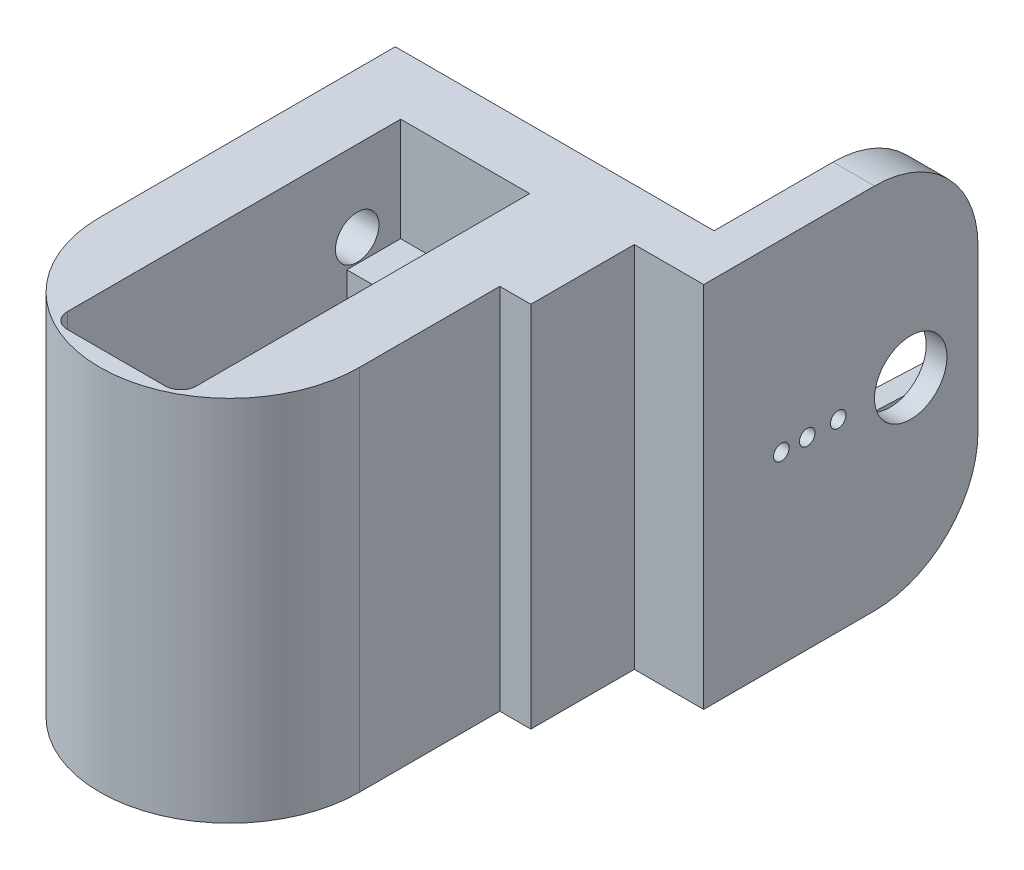
SolidWorks part; units mm, degrees
ref_plane "Front Plane" through (0, 0, 0) normal (0, 0, 1) x (1, 0, 0)
ref_plane "Top Plane" through (0, 0, 0) normal (0, 1, 0) x (1, 0, 0)
ref_plane "Right Plane" through (0, 0, 0) normal (1, 0, 0) x (0, 0, -1)
sketch "Sketch4" plane through (0, 0, 0) normal (0, 0, 1) x (1, 0, 0)
  line L1 (-6.23, -9.975) -> (6.23, -9.975)
  line L2 (-6.23, -9.975) -> (-6.23, 7.275)
  line L3 (-6.23, 7.275) -> (6.23, 7.275)
  line L4 (6.23, -9.975) -> (6.23, 7.275)
  point P4 (0, 7.275)
  dimension "D1" = 12.46
  dimension "D2" = 17.25
  dimension "D3" = 9.975
extrude "Boss-Extrude3" add sketch "Sketch4" along normal blind 6
sketch "Sketch8" plane through (0, -9.975, 0) normal (0, -1, 0) x (-1, 0, 0)
  circle A0 centre (0, -23.55) radius 12.5468
  circle A1 centre (0, -23.55) radius 11.15
  dimension "D1" = 22.3
  dimension "D2" = 23.55
extrude "Boss-Extrude6" add sketch "Sketch8" along normal blind 8.3 and the other way up to surface (17.25 mm away) other way up to face at (0, 7.275, 3)
sketch "Sketch5" plane through (0, 7.275, 0) normal (0, 1, 0) x (1, 0, 0)
  line L8 (12.5468, -23.55) -> (12.5468, 0)
  line L9 (12.5468, 0) -> (6.23, 0)
  line L10 (-12.5468, -23.55) -> (-12.5468, 0)
  line L11 (-12.5468, 0) -> (-6.23, 0)
  line L12 (-6.23, 0) -> (-6.23, -29.7)
  line L14 (6.23, -29.7) -> (6.23, 0)
  line L15 (-6.23, -29.7) -> (6.23, -29.7)
  line L16 (6.23, -6) -> (-6.23, -6) construction
  circle A0 centre (0, -23.55) radius 12.5468 construction
  arc A1 (-12.5468, -23.55) -> (12.5468, -23.55) centre (0, -23.55) ccw
  dimension "D1" = 23.7
  dimension "D2" = 23.55
extrude "Boss-Extrude4" add sketch "Sketch5" against normal up to surface (17.25 mm away) up to face at (0, -9.975, 3)
sketch "Sketch6" plane through (0, 7.275, 0) normal (0, 1, 0) x (1, 0, 0)
  line L0 (6.23, -6) -> (-6.23, -6) construction
  line L3 (6.23, -29.7) -> (-6.23, -29.7) construction
  circle A0 centre (0, -3.6) radius 0.75
  circle A1 centre (0, -32.1) radius 0.75
  dimension "D1" = 1.5
  dimension "D3" = 1.5
  dimension "D2" = 2.4
  dimension "D4" = 2.4
extrude "Cut-Extrude1" cut sketch "Sketch6" against normal blind 5
chamfer "Chamfer1" distance 0.5 angle 60 2 edges at (0, 7.275, 4.35) (0, 7.275, 32.85)
sketch "Sketch10" plane through (0, 7.275, 0) normal (0, 1, 0) x (1, 0, 0)
  line L1 (-6.23, -6) -> (6.23, -6)
  line L2 (-6.23, -6) -> (-6.23, -29.7)
  line L3 (-6.23, -29.7) -> (6.23, -29.7)
  line L4 (6.23, -6) -> (6.23, -29.7)
extrude "Cut-Extrude3" cut sketch "Sketch10" against normal up to surface (17.25 mm away) up to face at (0, -9.975, 27.1007)
ref_plane "Plane1" through (0, 0, 36.0968) normal (0, 0, 1) x (1, 0, 0)
sketch "Sketch13" plane through (0, -18.275, 0) normal (0, -1, 0) x (1, 0, 0)
  line L0 (-12.5468, 23.55) -> (-12.5468, 0)
  line L1 (-12.5468, 0) -> (12.5468, 0)
  line L2 (12.5468, 0) -> (12.5468, 23.55)
  arc A0 (-12.5468, 23.55) -> (12.5468, 23.55) centre (0, 23.55) ccw
  point P3 (0, 0)
extrude "Boss-Extrude7" add sketch "Sketch13" against normal up to surface (8.3 mm away) up to face at (0, -9.975, 27.1007)
sketch "Sketch15" plane through (0, 7.275, 0) normal (0, 1, 0) x (1, 0, 0)
  line L0 (-12.5468, 0) -> (12.5468, 0)
  line L1 (12.5468, 0) -> (12.5468, -23.55)
  line L2 (-12.5468, 0) -> (-12.5468, -23.55)
  line L3 (6.23, -6) -> (6.23, -29.7) construction
  line L4 (-6.23, -0.8) -> (6.23, -0.8)
  line L5 (-6.23, -0.8) -> (-6.23, -33)
  line L6 (-4.73, -34.5) -> (4.73, -34.5)
  line L7 (6.23, -0.8) -> (6.23, -33)
  arc A0 (-12.5468, -23.55) -> (12.5468, -23.55) centre (0, -23.55) ccw
  circle A1 centre (0, -3.6) radius 0.75 construction
  arc A2 (4.73, -34.5) -> (6.23, -33) centre (4.73, -33) ccw
  arc A3 (-6.23, -33) -> (-4.73, -34.5) centre (-4.73, -33) ccw
  point P15 (0, -0.8)
  dimension "D1" = 0.8
  dimension "D3" = 1.5
  dimension "D2" = 2.8
  dimension "D4" = 0
  dimension "D5" = 34.5
extrude "Boss-Extrude9" add sketch "Sketch15" along normal blind 10
sketch "Sketch20" plane through (0, -18.275, 0) normal (0, -1, 0) x (1, 0, 0)
  circle A0 centre (0, 23.55) radius 7.15
  circle A1 centre (0, 23.55) radius 11.15
  circle A2 centre (0, 23.55) radius 11.15 construction
  dimension "D1" = 14.3
extrude "Boss-Extrude11" add sketch "Sketch20" against normal up to surface (8.3 mm away) up to face at (0, -9.975, 27.1007)
sketch "Sketch21" plane through (0, -18.275, 0) normal (0, -1, 0) x (1, 0, 0)
  circle A0 centre (0, 23.55) radius 7.15
  circle A1 centre (0, 23.55) radius 10.15
  circle A2 centre (0, 23.55) radius 7.15 construction
  dimension "D1" = 20.3
extrude "Cut-Extrude7" cut sketch "Sketch21" against normal blind 1.3
sketch "Sketch11" plane through (0, 0, 29.7) normal (0, 0, 1) x (1, 0, 0)
  line L1 (-5, -9.975) -> (5, -9.975)
  line L2 (-5, -9.975) -> (-5, -11.975)
  line L3 (-5, -11.975) -> (5, -11.975)
  line L4 (5, -9.975) -> (5, -11.975)
  line L5 (-3.6469, -9.975) -> (3.6469, -9.975) construction
  point P4 (0, -9.975)
  dimension "D1" = 0
  dimension "D2" = 10
  dimension "D3" = 2
extrude "Cut-Extrude4" cut sketch "Sketch11" against normal up to surface (23.7 mm away) up to face at (0, -1.35, 6)
sketch "Sketch25" plane through (0, -18.275, 0) normal (0, -1, 0) x (1, 0, 0)
  line L0 (6.23, 20.0415) -> (6.23, 6) construction
  line L1 (-6.23, 6) -> (6.23, 6)
  line L2 (-6.23, 6) -> (-6.23, 12)
  line L3 (-6.23, 12) -> (6.23, 12)
  line L4 (6.23, 6) -> (6.23, 12)
  dimension "D1" = 6
extrude "Cut-Extrude8" cut sketch "Sketch25" against normal up to next
sketch "Sketch17" plane through (0, 17.275, 0) normal (0, 1, 0) x (1, 0, 0)
  line L0 (22.25, 26.5) -> (22.25, 0)
  line L1 (22.25, 0) -> (-22.25, 0)
  line L2 (-22.25, 0) -> (-22.25, 26.5)
  line L3 (-22.25, 26.5) -> (-18.25, 26.5)
  line L4 (-18.25, 26.5) -> (-18.25, 5)
  line L5 (-18.25, 5) -> (18.25, 5)
  line L6 (18.25, 5) -> (18.25, 26.5)
  line L7 (18.25, 26.5) -> (22.25, 26.5)
  point P2 (0, 5)
  point P10 (0, 0)
  dimension "D1" = 4
  dimension "D2" = 36.5
  dimension "D3" = 0
  dimension "D4" = 26.5
  dimension "D5" = 5
extrude "Boss-Extrude10" add sketch "Sketch17" against normal up to surface (35.55 mm away) up to face at (0, -18.275, 9)
sketch "Sketch18" plane through (18.25, 0, 0) normal (-1, 0, 0) x (0, 0, 1)
  line L0 (-26.5, -18.275) -> (-26.5, 17.275) construction
  line L1 (-26.5, 5.2191) -> (-5, 5.2191)
  line L2 (-26.5, 5.2191) -> (-26.5, -6.2191)
  line L3 (-26.5, -6.2191) -> (-5, -6.2191)
  line L4 (-5, 5.2191) -> (-5, -6.2191)
  line L5 (-5, -18.275) -> (-5, 17.275) construction
  point P6 (-26.5, -0.5)
  point P7 (-26.5, -0.5)
  dimension "D1" = 0
extrude "Cut-Extrude5" cut sketch "Sketch18" against normal blind 2
sketch "Sketch19" plane through (20.25, 0, 0) normal (-1, 0, 0) x (0, 0, 1)
  line L0 (-26.5, -18.275) -> (-26.5, 17.275) construction
  circle A0 centre (-20, -0.5) radius 3.5
  point P4 (-26.5, -0.5)
  dimension "D1" = 7
  dimension "D2" = 6.5
  dimension "D3" = 0
extrude "Cut-Extrude6" cut sketch "Sketch19" against normal through all both and the other way through all
fillet "Fillet1" radius 10 4 edges at (20.25, 17.275, -26.5) (20.25, -18.275, -26.5) (-20.25, 17.275, -26.5) (-20.25, -18.275, -26.5)
ref_plane "Plane2" through (0, 0, 0) normal (1, 0, 0) x (0, 0, -1)
ref_plane "Plane3" through (0, -0.5, 0) normal (0, -1, 0) x (-1, 0, 0)
sketch "Sketch22" plane through (-22.25, 0, 0) normal (-1, 0, 0) x (0, 0, 1)
  circle A0 centre (-20, -0.5) radius 6.5
  dimension "D1" = 13
extrude "Boss-Extrude12" add sketch "Sketch22" against normal blind 5
sketch "Sketch23" plane through (-17.25, 0, 0) normal (1, 0, 0) x (0, 0, -1)
  circle A0 centre (20, -0.5) radius 5.85
  dimension "D1" = 11.7
extrude "Boss-Extrude13" add sketch "Sketch23" along normal blind 5
fillet "Fillet2" radius 1 1 edges at (-12.25, -0.5, -25.85)
sketch "Sketch26" plane through (20.25, 0, 0) normal (-1, 0, 0) x (0, 0, 1)
  line L0 (-5, 2) -> (-20, 2.6585)
  line L1 (-5, -18.275) -> (-5, 17.275) construction
  line L4 (-5, 5.2191) -> (-5, 2)
  line L6 (-26.5, 5.2191) -> (-5, 5.2191)
  line L7 (-20, -3.6585) -> (-5, -3)
  line L8 (-5, -3) -> (-5, -6.2191)
  line L9 (-24.475, -0.5) -> (24.475, -0.5) construction
  line L11 (-26.5, -6.2191) -> (-5, -6.2191)
  line L12 (-20, 2.6585) -> (-26.5, 2.9439)
  line L13 (-20, -3.6585) -> (-26.5, -3.9438)
  line L14 (-26.5, -3.9438) -> (-26.5, -6.2191)
  line L16 (-26.5, 2.9439) -> (-26.5, 5.2191)
  line L18 (-26.5, -8.275) -> (-26.5, 7.275) construction
  circle A0 centre (-20, -0.5) radius 3.5 construction
  dimension "D1" = 5
  dimension "D2" = 2.5
  dimension "D3" = 0
  dimension "D4" = 6.317
  dimension "D5" = 3.1585
  dimension "D6" = 180
  dimension "D7" = 180
extrude "Boss-Extrude14" add sketch "Sketch26" along normal up to surface (2 mm away) up to face at (18.25, 10.8669, -16.3142)
sketch "Sketch27" plane through (22.25, 0, 0) normal (1, 0, 0) x (0, 0, -1)
  line L0 (-24.475, -0.5) -> (24.475, -0.5) construction
  circle A0 centre (10, -0.5) radius 0.75
  circle A1 centre (20, -0.5) radius 3.5 construction
  circle A2 centre (7.5, -0.5) radius 0.75
  circle A3 centre (13, -0.5) radius 0.75
  dimension "D2" = 1.5
  dimension "D4" = 12.5
  dimension "D1" = 10
  dimension "D3" = 7
extrude "Cut-Extrude9" cut sketch "Sketch27" against normal up to next
sketch "Sketch28" plane through (0, -18.275, 0) normal (0, -1, 0) x (1, 0, 0)
  line L0 (-12.5468, 23.55) -> (-12.5468, -11.5534)
  line L5 (-12.5468, -11.5534) -> (-1.7209, -11.5534)
  line L6 (-1.7209, -11.5534) -> (-1.7209, -30.3021)
  line L7 (-1.7209, -30.3021) -> (-26.8097, -30.3021)
  line L8 (-26.8097, -30.3021) -> (-26.8097, 23.55)
  line L9 (-26.8097, 23.55) -> (-12.5468, 23.55)
extrude "Cut-Extrude10" cut sketch "Sketch28" against normal through all
sketch "Sketch29" plane through (-12.5468, 0, 0) normal (-1, 0, 0) x (0, 0, 1)
  line L0 (-5, 17.275) -> (-5, -18.275) construction
  line L3 (-26.5, 2.9438) -> (-26.5, -3.9438) construction
  circle A0 centre (5, 9.5) radius 2.1
  circle A1 centre (5, -10.5) radius 2.1
  circle A2 centre (5, -0.5) radius 3.2
  point P12 (-26.5, -0.5)
  dimension "D1" = 4.2
  dimension "D2" = 4.2
  dimension "D6" = 6.4
  dimension "D3" = 20
  dimension "D4" = 10
  dimension "D7" = 10
extrude "Cut-Extrude11" cut sketch "Sketch29" against normal blind 7
fillet "Fillet3" radius 1 2 edges at (-12.5468, -10.5, 7.1) (-12.5468, 9.5, 7.1)
sketch "Sketch31" plane through (12.5468, 0, 0) normal (1, 0, 0) x (0, 0, -1)
  line L0 (0, -18.275) -> (-23.55, -18.275) construction
  line L1 (0, 17.275) -> (-10, 17.275)
  line L2 (0, 17.275) -> (0, -18.275)
  line L3 (0, -18.275) -> (-10, -18.275)
  line L4 (-10, 17.275) -> (-10, -18.275)
  dimension "D1" = 10
extrude "Boss-Extrude15" add sketch "Sketch31" along normal blind 3
